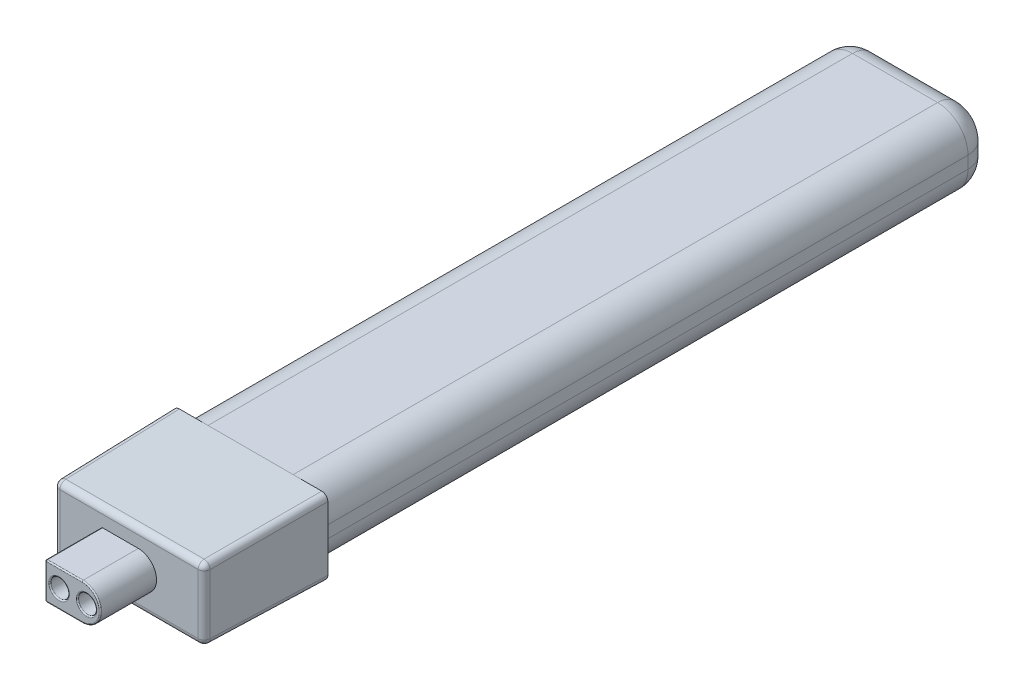
SolidWorks part; units mm, degrees
ref_plane "Front Plane" through (0, 0, 0) normal (0, 0, 1) x (1, 0, 0)
ref_plane "Top Plane" through (0, 0, 0) normal (0, 1, 0) x (1, 0, 0)
ref_plane "Right Plane" through (0, 0, 0) normal (1, 0, 0) x (0, 0, -1)
sketch "Sketch1" plane through (0, 0, 0) normal (0, 0, 1) x (1, 0, 0)
  line L0 (-3, 0) -> (3, 0) construction
  line L5 (-3, 3) -> (3, 3) construction
  line L6 (-3, -3) -> (3, -3) construction
  line L8 (-3.5, -3) -> (3.5, -3)
  line L9 (-6, -0.5) -> (-6, 0.5)
  line L10 (-3.5, 3) -> (3.5, 3)
  line L11 (6, -0.5) -> (6, 0.5)
  line L12 (-6, -3) -> (6, 3) construction
  line L13 (-6, 3) -> (6, -3) construction
  arc A0 (-3, 3) -> (-3, -3) centre (-3, 0) ccw construction
  arc A1 (3, -3) -> (3, 3) centre (3, 0) ccw construction
  arc A2 (3.5, -3) -> (6, -0.5) centre (3.5, -0.5) ccw
  arc A3 (-6, 0.5) -> (-3.5, 3) centre (-3.5, 0.5) cw
  arc A4 (-3.5, -3) -> (-6, -0.5) centre (-3.5, -0.5) cw
  arc A5 (3.5, 3) -> (6, 0.5) centre (3.5, 0.5) cw
  point P2 (0, 0)
  point P8 (-6, 0)
  point P9 (6, 0)
  point P10 (0, 0)
  dimension "D3" = 2.5
  dimension "D1" = 6
  dimension "D2" = 12
extrude "Boss-Extrude1" add sketch "Sketch1" along normal mid plane 55
sketch "Sketch2" plane through (0, 0, 27.5) normal (0, 0, 1) x (1, 0, 0)
  line L1 (-6.35, 3) -> (6.35, 3)
  line L2 (-6.35, 3) -> (-6.35, -3.25)
  line L3 (-6.35, -3.25) -> (6.35, -3.25)
  line L4 (6.35, 3) -> (6.35, -3.25)
  line L5 (-6.35, 3) -> (6.35, -3.25) construction
  line L6 (-6.35, -3.25) -> (6.35, 3) construction
  line L8 (3.5, 3) -> (-3.5, 3) construction
  point P0 (0, -0.125)
  dimension "D1" = 12.7
  dimension "D2" = 6.25
extrude "Boss-Extrude2" add sketch "Sketch2" along normal blind 10 draft 1
sketch "Sketch3" plane through (0, 0, 27.5) normal (0, 0, -1) x (-1, 0, 0)
  line L0 (-6.35, -3.25) -> (-6.35, 3) construction
  line L1 (-6.35, 2.025) -> (-6, 2.025)
  line L2 (-6.35, 2.025) -> (-6.35, -2.275)
  line L3 (-6.35, -2.275) -> (-6, -2.275)
  line L4 (-6, 2.025) -> (-6, -2.275)
  line L5 (-6.35, -3.25) -> (6.35, 3) construction
  line L6 (-6, -0.5) -> (-6, 0.5) construction
  point P10 (-6, -0.125)
  point P11 (0, -0.125)
  dimension "D1" = 4.3
extrude "Boss-Extrude3" [suppressed] add sketch "Sketch3" along normal blind 4
mirror "Mirror1" [suppressed] about plane through (0, 0, 0) normal (1, 0, 0)
fillet "Fillet2" radius 2 8 edges at (6, 0, -27.5) (5.2678, 2.2678, -27.5) (0, 3, -27.5) (-5.2678, 2.2678, -27.5) (-6, 0, -27.5) (-5.2678, -2.2678, -27.5) (0, -3, -27.5) (5.2678, -2.2678, -27.5)
sketch "Sketch4" plane through (0, 0, 37.5) normal (0, 0, 1) x (1, 0, 0)
  line L8 (6.1754, 2.8254) -> (-6.1754, -3.0754) construction
  line L13 (-2.265, -0.125) -> (-1.1325, -0.125) construction
  line L14 (-2.265, 1.375) -> (0.765, 1.375)
  line L19 (-2.265, 1.375) -> (-2.265, -1.625)
  line L20 (-2.265, -1.625) -> (0.765, -1.625)
  line L21 (0.765, 1.375) -> (0.765, -1.625) construction
  line L22 (-1.1325, -0.125) -> (0, -0.125) construction
  line L23 (1.1325, -0.125) -> (2.265, -0.125) construction
  line L24 (0, -0.125) -> (1.1325, -0.125) construction
  arc A0 (0.765, 1.375) -> (0.765, -1.625) centre (0.765, -0.125) cw
  circle A1 centre (-1.1325, -0.125) radius 0.75
  circle A2 centre (1.1325, -0.125) radius 0.75
  point P3 (0, -0.125)
  point P10 (2.265, -0.125)
  dimension "D3" = 1.5
  dimension "D1" = 4.53
  dimension "D2" = 3
extrude "Boss-Extrude4" add sketch "Sketch4" along normal blind 4.62
fillet "Fillet3" radius 0.5 8 edges at (6.2627, 2.9127, 32.5) (6.1754, -0.125, 37.5) (6.2627, -3.1627, 32.5) (0, -3.0754, 37.5) (-6.2627, -3.1627, 32.5) (0, 2.8254, 37.5) (-6.1754, -0.125, 37.5) (-6.2627, 2.9127, 32.5)
fillet "Fillet4" radius 0.1 8 edges at (-0.75, -1.625, 42.12) (-0.75, 1.375, 42.12) (-0.3825, -0.125, 42.12) (1.8825, -0.125, 42.12) (-2.265, -1.625, 39.81) (-2.265, -0.125, 42.12) (-2.265, 1.375, 39.81) (2.265, -0.125, 42.12)
